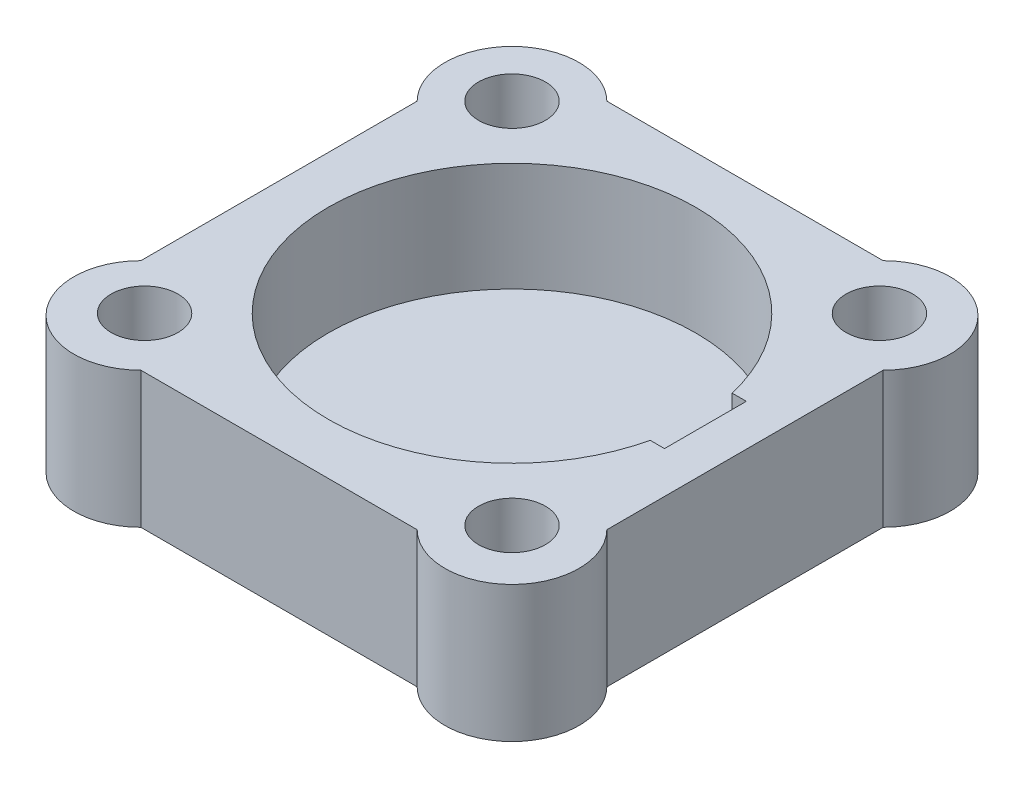
SolidWorks part; units mm, degrees
ref_plane "Front Plane" through (0, 0, 0) normal (0, 0, 1) x (1, 0, 0)
ref_plane "Top Plane" through (0, 0, 0) normal (0, 1, 0) x (1, 0, 0)
ref_plane "Right Plane" through (0, 0, 0) normal (1, 0, 0) x (0, 0, -1)
sketch "Sketch1" plane through (0, 0, 0) normal (0, 1, 0) x (1, 0, 0)
  line L0 (-15.0227, 25.4773) -> (-25.4773, 15.0227) construction
  line L1 (-20.25, -20.25) -> (20.25, -20.25) construction
  line L2 (-20.25, -20.25) -> (-20.25, 20.25) construction
  line L3 (-20.25, 20.25) -> (20.25, 20.25) construction
  line L4 (20.25, -20.25) -> (20.25, 20.25) construction
  line L5 (-20.25, -20.25) -> (20.25, 20.25) construction
  line L6 (-20.25, 20.25) -> (20.25, -20.25) construction
  line L7 (-25.4773, -15.4332) -> (-25.4773, 15.0227)
  line L8 (-15.0227, 25.4773) -> (15.4332, 25.4773)
  line L9 (25.8878, 15.0227) -> (25.8878, -15.4332)
  line L10 (15.4332, -25.8878) -> (-15.0227, -25.8878)
  circle A0 centre (0, 0) radius 20.25
  circle A1 centre (-20.25, 20.25) radius 3.6822
  circle A2 centre (20.25, 20.25) radius 3.6822
  circle A3 centre (20.25, -20.25) radius 3.6822
  circle A4 centre (-20.25, -20.25) radius 3.6822
  arc A5 (-25.4773, 15.0227) -> (-15.0227, 25.4773) centre (-20.25, 20.25) cw
  arc A6 (-15.0227, -25.8878) -> (-25.4773, -15.4332) centre (-20.25, -20.6605) cw
  arc A7 (25.8878, -15.4332) -> (15.4332, -25.8878) centre (20.6605, -20.6605) cw
  arc A8 (15.4332, 25.4773) -> (25.8878, 15.0227) centre (20.6605, 20.25) cw
  point P14 (-20.25, 20.25)
  dimension "D1" = 40.5
  dimension "D2" = 4
extrude "Boss-Extrude1" add sketch "Sketch1" along normal blind 15 contours A0
sketch "Sketch2" plane through (0, 0, 0) normal (0, -1, 0) x (1, 0, 0)
  circle A0 centre (0, 0) radius 20.25
extrude "Boss-Extrude2" add sketch "Sketch2" against normal blind 3
sketch "Sketch3" plane through (0, 3, 0) normal (0, 1, 0) x (1, 0, 0)
  line L1 (21.3201, -4.5109) -> (19.1799, -4.5109)
  line L2 (21.3201, -4.5109) -> (21.3201, 4.5109)
  line L3 (21.3201, 4.5109) -> (19.1799, 4.5109)
  line L4 (19.1799, -4.5109) -> (19.1799, 4.5109)
  line L5 (21.3201, -4.5109) -> (19.1799, 4.5109) construction
  line L6 (21.3201, 4.5109) -> (19.1799, -4.5109) construction
  circle A0 centre (0, 0) radius 20.25 construction
  circle A1 centre (0, 0) radius 20.25 construction
  point P0 (20.25, 0)
extrude "Cut-Extrude1" cut sketch "Sketch3" against normal through all and the other way through all contours L4 L3 L2 L1
